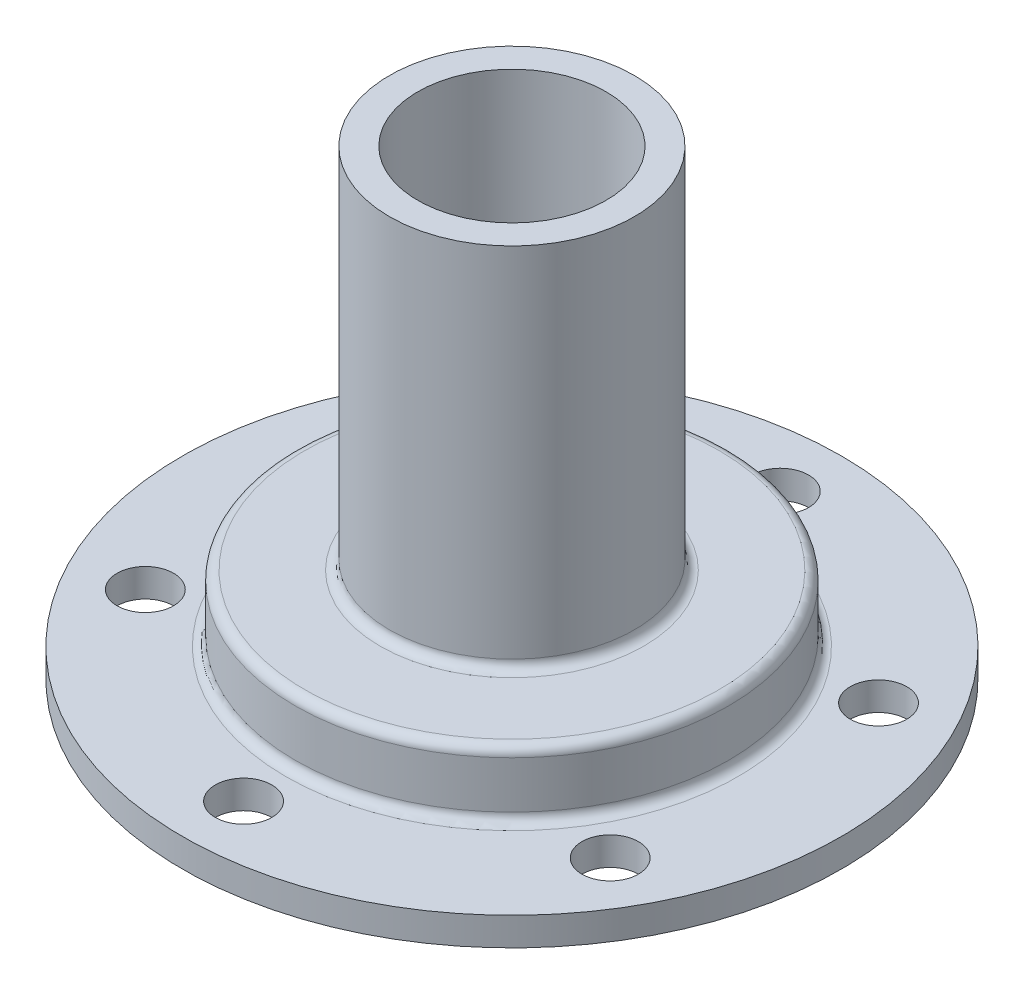
SolidWorks part; units mm, degrees
material "普通碳钢"
ref_plane "前视基准面" through (0, 0, 0) normal (0, 0, 1) x (1, 0, 0)
ref_plane "上视基准面" through (0, 0, 0) normal (0, 1, 0) x (1, 0, 0)
ref_plane "右视基准面" through (0, 0, 0) normal (1, 0, 0) x (0, 0, -1)
sketch "草图1" plane through (0, 0, 0) normal (0, 0, 1) x (1, 0, 0)
  line L0 (0, 0) -> (0, 81.5505) construction
  line L3 (20, 0) -> (35, 0)
  line L4 (35, 0) -> (35, 3)
  line L5 (35, 3) -> (24, 3)
  line L6 (23, 4) -> (23, 9)
  line L7 (22, 10) -> (14, 10)
  line L8 (13, 11) -> (13, 49)
  line L9 (13, 49) -> (10, 49)
  line L10 (10, 49) -> (10, 7)
  line L11 (10, 7) -> (19, 7)
  line L12 (20, 6) -> (20, 0)
  arc A0 (24, 3) -> (23, 4) centre (24, 4) cw
  arc A1 (19, 7) -> (20, 6) centre (19, 6) cw
  arc A2 (23, 9) -> (22, 10) centre (22, 9) ccw
  arc A3 (14, 10) -> (13, 11) centre (14, 11) cw
  dimension "D9" = 1
  dimension "D2" = 3
  dimension "D3" = 3
  dimension "D4" = 3
  dimension "D5" = 13
  dimension "D6" = 3
  dimension "D7" = 42
  dimension "D8" = 10
  dimension "D10" = 20
  dimension "D11" = 35
revolve "旋转1" add sketch "草图1" angle 360 about L0
sketch "草图2" plane through (0, 3, 0) normal (0, 1, 0) x (1, 0, 0)
  circle A0 centre (0, 28.5) radius 3
  circle A1 centre (24.6817, 14.25) radius 3
  circle A2 centre (24.6817, -14.25) radius 3
  circle A3 centre (0, -28.5) radius 3
  circle A4 centre (-24.6817, -14.25) radius 3
  circle A5 centre (-24.6817, 14.25) radius 3
  point P15 (0, 0)
  dimension "D1" = 28.5
  dimension "D3" = 6
  dimension "D2" = 6
extrude "切除-拉伸1" cut sketch "草图2" against normal through all
sketch "草图3" plane through (0, 0, 0) normal (1, 0, 0) x (0, 0, -1)
  line L0 (0, 10) -> (0, 34) construction
  line L1 (22, 10) -> (-22, 10) construction
  line L2 (13, 49) -> (-13, 49) construction
  circle A0 centre (0, 34) radius 2.5
  dimension "D1" = 15
  dimension "D2" = 5
extrude "切除-拉伸2" cut sketch "草图3" against normal through all
equation "\"32。5\"=55"
